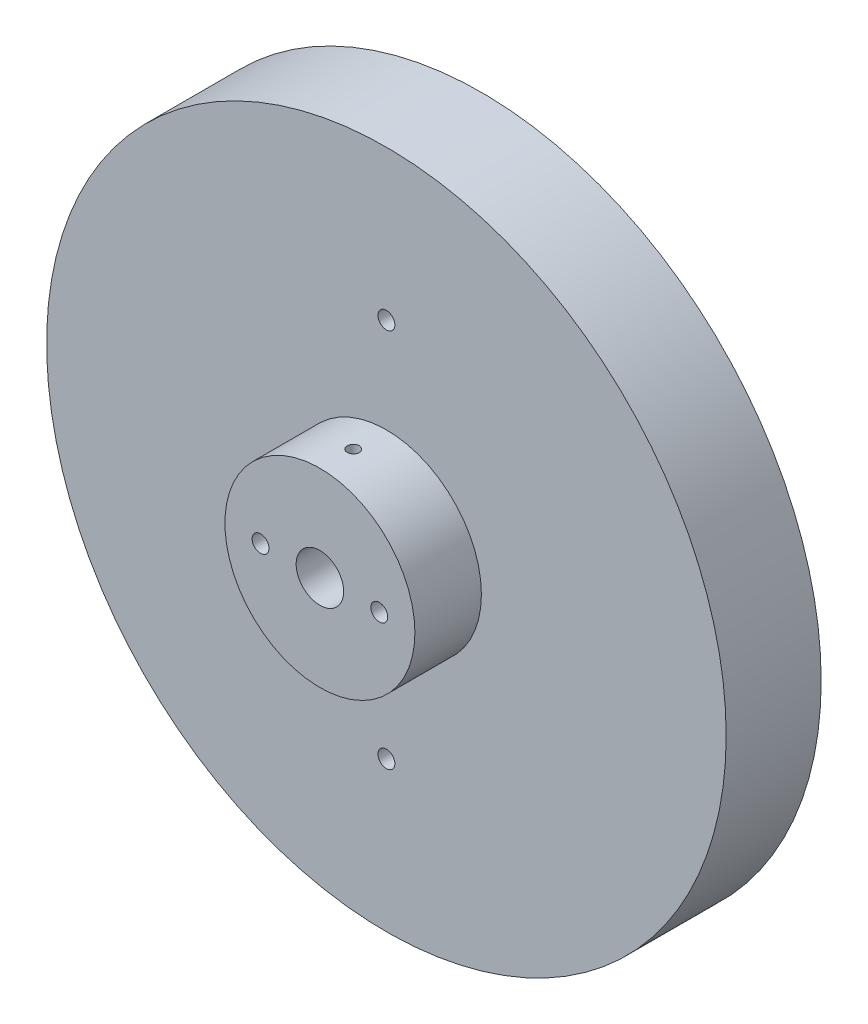
SolidWorks part; units mm, degrees
ref_plane "Front Plane" through (0, 0, 0) normal (0, 0, 1) x (1, 0, 0)
ref_plane "Top Plane" through (0, 0, 0) normal (0, 1, 0) x (1, 0, 0)
ref_plane "Right Plane" through (0, 0, 0) normal (1, 0, 0) x (0, 0, -1)
sketch "Sketch2" plane through (0, 0, 0) normal (0, 0, 1) x (1, 0, 0)
  circle A0 centre (0, 0) radius 45.4279
  dimension "D1" = 90.8558
extrude "Boss-Extrude1" add sketch "Sketch2" along normal blind 12.7
sketch "Sketch3" plane through (0, 0, 12.7) normal (0, 0, 1) x (1, 0, 0)
  circle A0 centre (0, 0) radius 12.7
  dimension "D1" = 25.4
extrude "Boss-Extrude2" add sketch "Sketch3" along normal blind 8.89
sketch "Sketch4" plane through (0, 0, 21.59) normal (0, 0, 1) x (1, 0, 0)
  line L0 (-7.9375, 0) -> (0, 0) construction
  line L1 (0, 0) -> (7.9375, 0) construction
  line L2 (-7.9375, 0) -> (-12.7, 0) construction
  line L3 (-7.9375, 0) -> (-3.175, 0) construction
  circle A0 centre (0, 0) radius 3.175
  circle A1 centre (-7.9375, 0) radius 1.1303
  circle A2 centre (7.9375, 0) radius 1.1303
  circle A3 centre (0, 0) radius 12.7 construction
  point P6 (0, 0)
  dimension "D1" = 6.35
  dimension "D3" = 2.2606
extrude "Cut-Extrude1" cut sketch "Sketch4" against normal through all
sketch "Sketch5" plane through (0, 0, 0) normal (0, 1, 0) x (1, 0, 0)
  line L0 (0, -17.145) -> (0, -21.59) construction
  line L1 (-12.7, -21.59) -> (12.7, -21.59) construction
  line L2 (-12.7, -12.7) -> (12.7, -12.7) construction
  line L3 (0, -17.145) -> (0, -12.7) construction
  circle A0 centre (0, -17.145) radius 0.7937
  dimension "D1" = 1.5875
extrude "Cut-Extrude2" cut sketch "Sketch5" against normal through all both and the other way through all
sketch "Sketch6" plane through (0, 0, 12.7) normal (0, 0, 1) x (1, 0, 0)
  circle A0 centre (0, 25.4) radius 1.1303
  circle A1 centre (0, -25.4) radius 1.1303
  dimension "D1" = 25.4
  dimension "D3" = 2.2606
  dimension "D2" = 25.4
extrude "Cut-Extrude3" cut sketch "Sketch6" against normal through all
